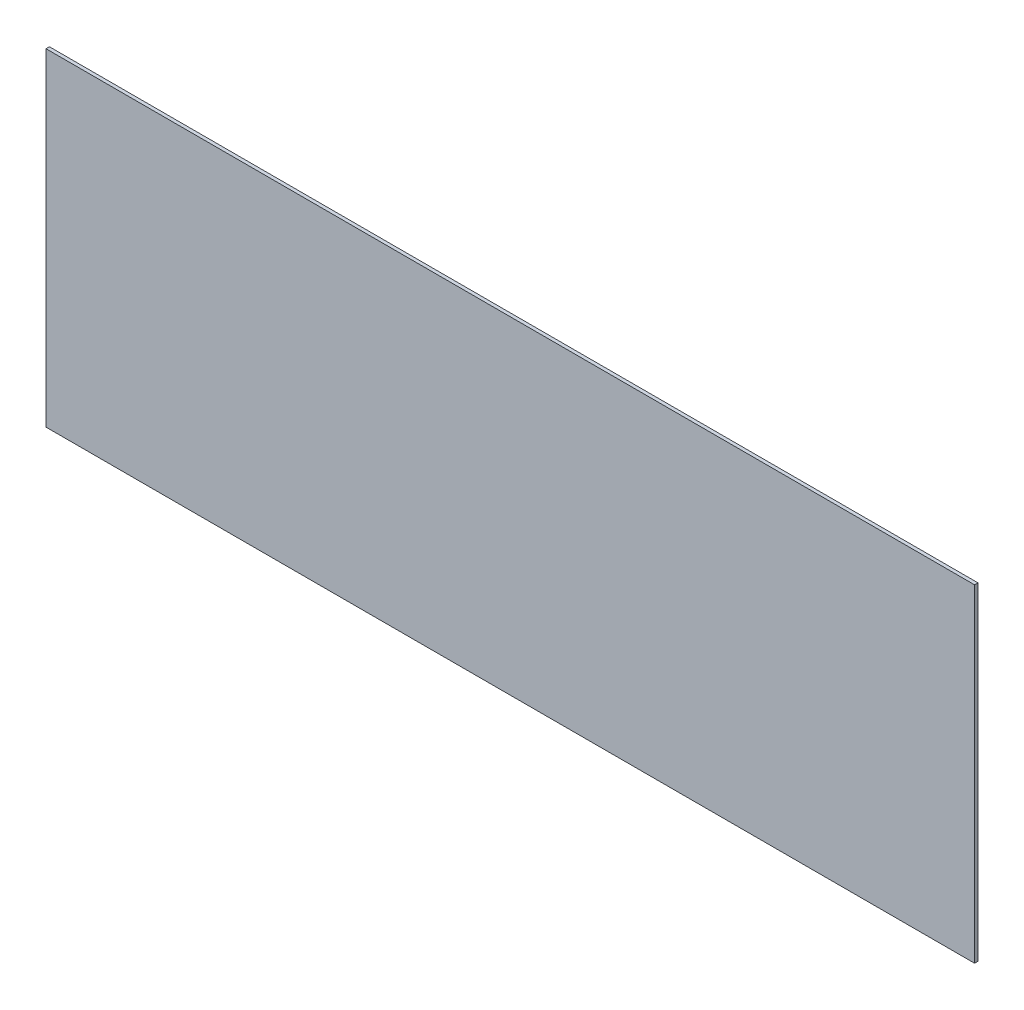
SolidWorks part; units mm, degrees
ref_plane "Front Plane" through (0, 0, 0) normal (0, 0, 1) x (1, 0, 0)
ref_plane "Top Plane" through (0, 0, 0) normal (0, 1, 0) x (1, 0, 0)
ref_plane "Right Plane" through (0, 0, 0) normal (1, 0, 0) x (0, 0, -1)
sketch "Sketch1" plane through (0, 0, 0) normal (0, 0, 1) x (1, 0, 0)
  line L0 (-431.8, 0) -> (431.8, 0) construction
  line L1 (-431.8, 152.4) -> (431.8, 152.4)
  line L2 (-431.8, 152.4) -> (-431.8, -152.4)
  line L3 (-431.8, -152.4) -> (431.8, -152.4)
  line L4 (431.8, 152.4) -> (431.8, -152.4)
  line L5 (0, 152.4) -> (0, -152.4) construction
  point P8 (0, 0)
  dimension "D1" = 863.6
  dimension "D2" = 304.8
extrude "Boss-Extrude1" add sketch "Sketch1" along normal blind 3.175
